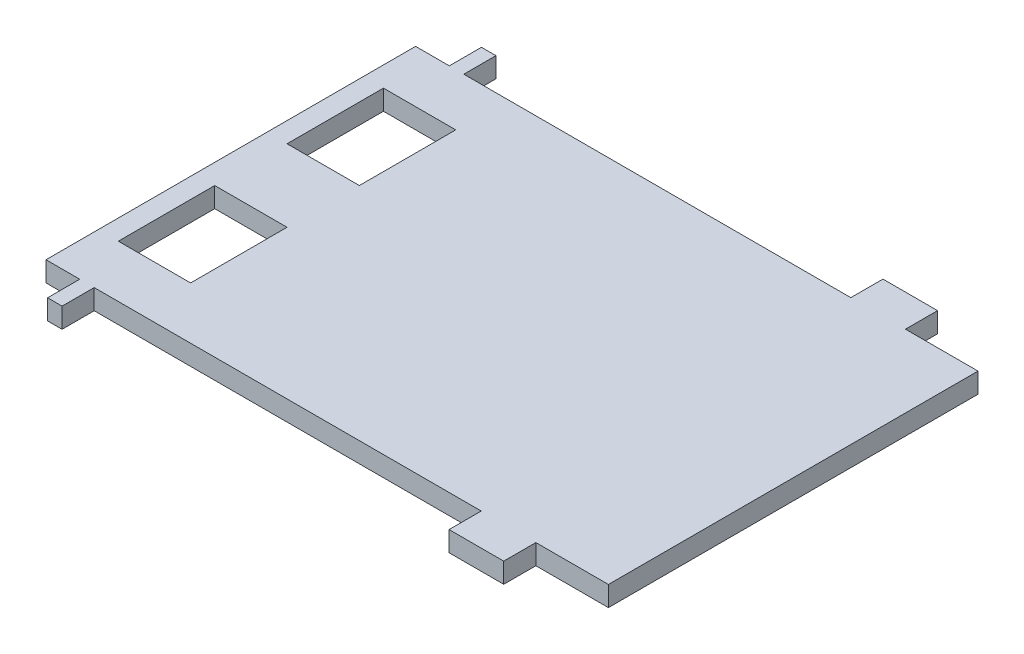
SolidWorks part; units mm, degrees
ref_plane "前视" through (0, 0, 0) normal (0, 0, 1) x (1, 0, 0)
ref_plane "上视" through (0, 0, 0) normal (0, 1, 0) x (1, 0, 0)
ref_plane "右视" through (0, 0, 0) normal (1, 0, 0) x (0, 0, -1)
sketch "草图1" plane through (0, 0, 0) normal (0, 1, 0) x (1, 0, 0)
  line L1 (-35, 27) -> (35, 27)
  line L2 (-35, 27) -> (-35, -27)
  line L3 (-35, -27) -> (35, -27)
  line L4 (35, 27) -> (35, -27)
  line L5 (-35, 27) -> (35, -27) construction
  line L6 (-35, -27) -> (35, 27) construction
  point P0 (0, 0)
  dimension "D1" = 70
  dimension "D2" = 54
extrude "凸台-拉伸1" add sketch "草图1" along normal blind 2.5
sketch "草图2" plane through (0, 2.5, 0) normal (0, 1, 0) x (1, 0, 0)
  line L0 (25.97, 27) -> (25.97, 23)
  line L1 (35, 27) -> (-35, 27) construction
  line L2 (25.97, 23) -> (35, 23)
  line L3 (35, -27) -> (35, 27) construction
  line L4 (35, 23) -> (35, 27)
  line L5 (35, 27) -> (25.97, 27)
  line L6 (19.17, 27) -> (19.17, 23)
  line L7 (-29, 23) -> (-29, 27)
  line L8 (19.17, 23) -> (-29, 23)
  line L9 (-29, 27) -> (19.17, 27)
  line L10 (-30.8, 27) -> (-30.8, 23)
  line L11 (-30.8, 23) -> (-35, 23)
  line L12 (-35, 27) -> (-35, -27) construction
  line L13 (-35, 23) -> (-35, 27)
  line L14 (-35, 27) -> (-30.8, 27)
  line L15 (0, 0) -> (-4.3874, 0) construction
  line L16 (-35, -23) -> (-35, -27)
  line L17 (-35, -27) -> (-30.8, -27)
  line L18 (-30.8, -27) -> (-30.8, -23)
  line L19 (-30.8, -23) -> (-35, -23)
  line L20 (25.97, -23) -> (35, -23)
  line L21 (35, -23) -> (35, -27)
  line L22 (35, -27) -> (25.97, -27)
  line L23 (25.97, -27) -> (25.97, -23)
  line L24 (19.17, -27) -> (19.17, -23)
  line L25 (-29, -23) -> (-29, -27)
  line L26 (-29, -27) -> (19.17, -27)
  line L27 (19.17, -23) -> (-29, -23)
  point P35 (-33.5, 17.8577)
  dimension "D1" = 4
  dimension "D2" = 9.03
  dimension "D3" = 6.8
  dimension "D5" = 1.8
extrude "切除-拉伸1" cut sketch "草图2" against normal through all
sketch "草图3" plane through (0, 2.5, 0) normal (0, 1, 0) x (1, 0, 0)
  line L0 (-29, 23) -> (19.17, 23) construction
  line L1 (-32.5, 16.5) -> (-23.5, 16.5)
  line L2 (-32.5, 16.5) -> (-32.5, 4.5)
  line L3 (-32.5, 4.5) -> (-23.5, 4.5)
  line L4 (-23.5, 16.5) -> (-23.5, 4.5)
  line L5 (-32.5, 16.5) -> (-23.5, 4.5) construction
  line L6 (-32.5, 4.5) -> (-23.5, 16.5) construction
  line L7 (-35, 23) -> (-35, -23) construction
  line L8 (0, 0) -> (-4.8571, 0) construction
  line L9 (-23.5, -16.5) -> (-23.5, -4.5)
  line L10 (-32.5, -4.5) -> (-23.5, -4.5)
  line L11 (-32.5, -16.5) -> (-32.5, -4.5)
  line L12 (-32.5, -16.5) -> (-23.5, -16.5)
  point P0 (-28, 10.5)
  dimension "D1" = 6.5
  dimension "D2" = 2.5
  dimension "D3" = 12
  dimension "D4" = 9
extrude "切除-拉伸2" cut sketch "草图3" against normal through all
